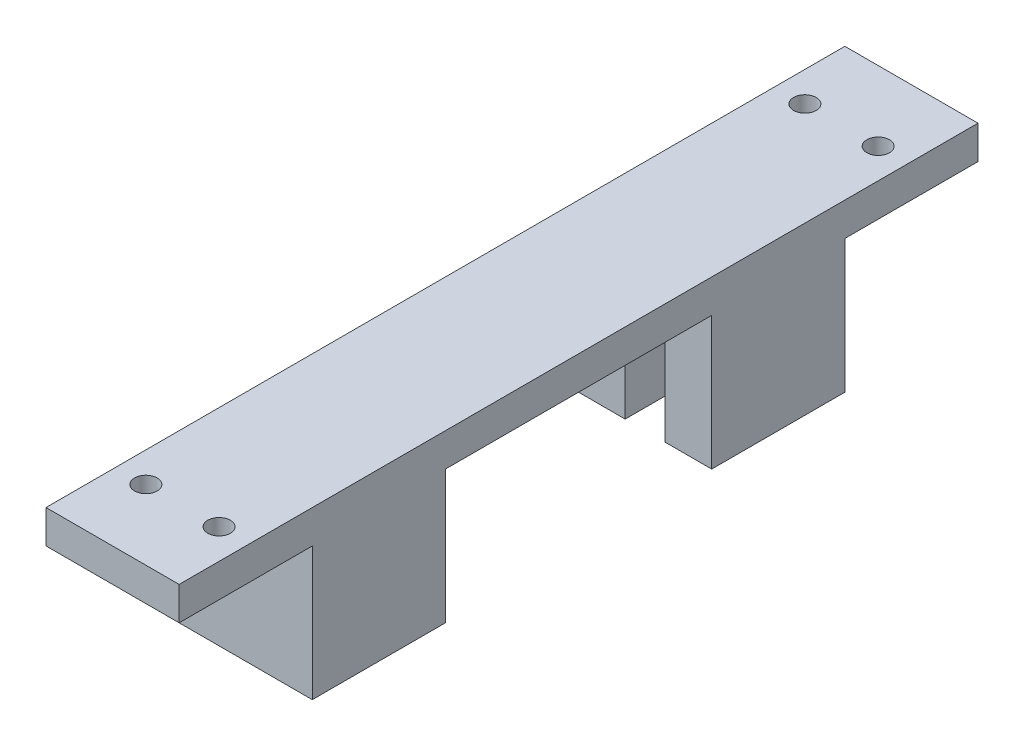
SolidWorks part; units mm, degrees
ref_plane "Front Plane" through (0, 0, 0) normal (0, 0, 1) x (1, 0, 0)
ref_plane "Top Plane" through (0, 0, 0) normal (0, 1, 0) x (1, 0, 0)
ref_plane "Right Plane" through (0, 0, 0) normal (1, 0, 0) x (0, 0, -1)
sketch "Sketch1" plane through (0, 0, 0) normal (0, 1, 0) x (1, 0, 0)
  line L1 (-10, -20) -> (10, -20)
  line L2 (-10, -20) -> (-10, 20)
  line L3 (-10, 20) -> (10, 20)
  line L4 (10, -20) -> (10, 20)
  line L5 (-10, -20) -> (10, 20) construction
  line L6 (-10, 20) -> (10, -20) construction
  point P0 (0, 0)
  dimension "D1" = 20
  dimension "D2" = 40
extrude "Boss-Extrude1" add sketch "Sketch1" along normal blind 5 contours L4 L3 L2 L1
sketch "Sketch2" plane through (0, 0, 0) normal (0, -1, 0) x (-1, 0, 0)
  line L0 (10, -20) -> (10, 20) construction
  line L1 (-10, 20) -> (10, 20)
  line L2 (-10, 20) -> (-10, 0)
  line L3 (-10, 0) -> (10, 0)
  line L4 (10, 20) -> (10, 0)
  dimension "D1" = 20
extrude "Boss-Extrude2" add sketch "Sketch2" along normal blind 20
sketch "Sketch3" plane through (0, -20, 0) normal (0, -1, 0) x (-1, 0, 0)
  line L0 (10, 20) -> (-10, 20) construction
  line L1 (-3, 20) -> (3, 20)
  line L2 (-3, 20) -> (-3, 4)
  line L3 (-3, 4) -> (3, 4)
  line L4 (3, 20) -> (3, 4)
  line L5 (-10, 20) -> (-10, 0) construction
  dimension "D1" = 6
  dimension "D2" = 16
  dimension "D3" = 7
extrude "Cut-Extrude1" cut sketch "Sketch3" against normal blind 20
hole_wizard "M3 Clearance Hole1" positions "Sketch5" profile "Sketch4" hole size "M3" standard "ANSI Metric"
sketch "Sketch5" plane through (0, 0, 0) normal (0, -1, 0) x (-1, 0, 0)
  line L0 (-10, 0) -> (10, 0) construction
  line L2 (-10, -20) -> (-10, 0) construction
  line L3 (10, -20) -> (10, 0) construction
  point P1 (-5.5, -9.5)
  point P3 (5.5, -9.5)
  dimension "D1" = 9.5
  dimension "D2" = 9.5
  dimension "D3" = 4.5
  dimension "D4" = 4.5
sketch "Sketch4" plane through (5.5, 0, 9.5) normal (1, 0, 0) x (0, 0, -1)
  line L0 (0, 0) -> (0, 6.0205)
  line L1 (0, 6.0205) -> (1.7, 4.999)
  line L2 (1.7, 4.999) -> (1.7, 0)
  line L5 (1.7, 0) -> (0, 0)
  line L10 (0, 6.0205) -> (-1.7, 4.999) construction
  line L11 (0, -6.35) -> (0, 107.95) construction
  dimension "Hole Dia." = 3.4
  dimension "Hole Depth" = 4.999
  dimension "Drill Angle" = 118
sketch "Sketch6" plane through (0, 0, -20) normal (0, 0, -1) x (-1, 0, 0)
  line L0 (-10, 5) -> (-10, -20) construction
  line L1 (10, 5) -> (-10, 5)
  line L2 (10, 5) -> (10, 0)
  line L3 (10, 0) -> (-10, 0)
  line L4 (-10, 5) -> (-10, 0)
extrude "Boss-Extrude3" add sketch "Sketch6" along normal blind 60
sketch "Sketch7" plane through (0, 0, -80) normal (0, 0, -1) x (-1, 0, 0)
  line L1 (-10, 5) -> (10, 5)
  line L2 (-10, 5) -> (-10, 0)
  line L3 (-10, 0) -> (10, 0)
  line L4 (10, 5) -> (10, 0)
extrude "Boss-Extrude4" add sketch "Sketch7" along normal blind 20
sketch "Sketch8" plane through (0, 0, 0) normal (0, -1, 0) x (-1, 0, 0)
  line L1 (-10, 100) -> (-10, 20) construction
  line L2 (-10, 60) -> (10, 60)
  line L3 (-10, 60) -> (-10, 80)
  line L5 (-10, 80) -> (10, 80)
  line L6 (10, 60) -> (10, 80)
  line L7 (10, 100) -> (10, 20) construction
  line L8 (-10, 100) -> (10, 100) construction
  dimension "D1" = 20
  dimension "D2" = 20
extrude "Boss-Extrude5" add sketch "Sketch8" along normal blind 20
sketch "Sketch9" plane through (0, -20, 0) normal (0, -1, 0) x (-1, 0, 0)
  line L1 (3, 60) -> (-3, 60)
  line L2 (3, 60) -> (3, 76)
  line L3 (3, 76) -> (-3, 76)
  line L4 (-3, 60) -> (-3, 76)
  line L8 (10, 60) -> (10, 80) construction
  line L9 (-10, 80) -> (-10, 60) construction
  line L10 (10, 80) -> (-10, 80) construction
  dimension "D1" = 7
  dimension "D2" = 7
  dimension "D3" = 4
extrude "Cut-Extrude2" cut sketch "Sketch9" against normal blind 20
hole_wizard "M3 Clearance Hole2" positions "Sketch11" profile "Sketch10" hole size "M3" standard "ANSI Metric" end condition through all
sketch "Sketch11" plane through (0, 0, 0) normal (0, -1, 0) x (-1, 0, 0)
  line L0 (10, 80) -> (-10, 80) construction
  line L1 (-10, 100) -> (-10, 80) construction
  line L2 (10, 100) -> (10, 80) construction
  point P0 (-5.5, 89.5)
  point P2 (5.5, 89.5)
  dimension "D1" = 9.5
  dimension "D2" = 9.5
  dimension "D3" = 4.5
  dimension "D4" = 4.5
sketch "Sketch10" plane through (5.5, 0, -89.5) normal (1, 0, 0) x (0, 0, -1)
  line L0 (0, 0) -> (0, 5)
  line L1 (0, 5) -> (1.7, 5)
  line L2 (1.7, 5) -> (1.7, 0)
  line L5 (1.7, 0) -> (0, 0)
  line L11 (0, -6.35) -> (0, 107.95) construction
  dimension "Thru Hole Dia." = 3.4
  dimension "Thru Hole Depth" = 5
